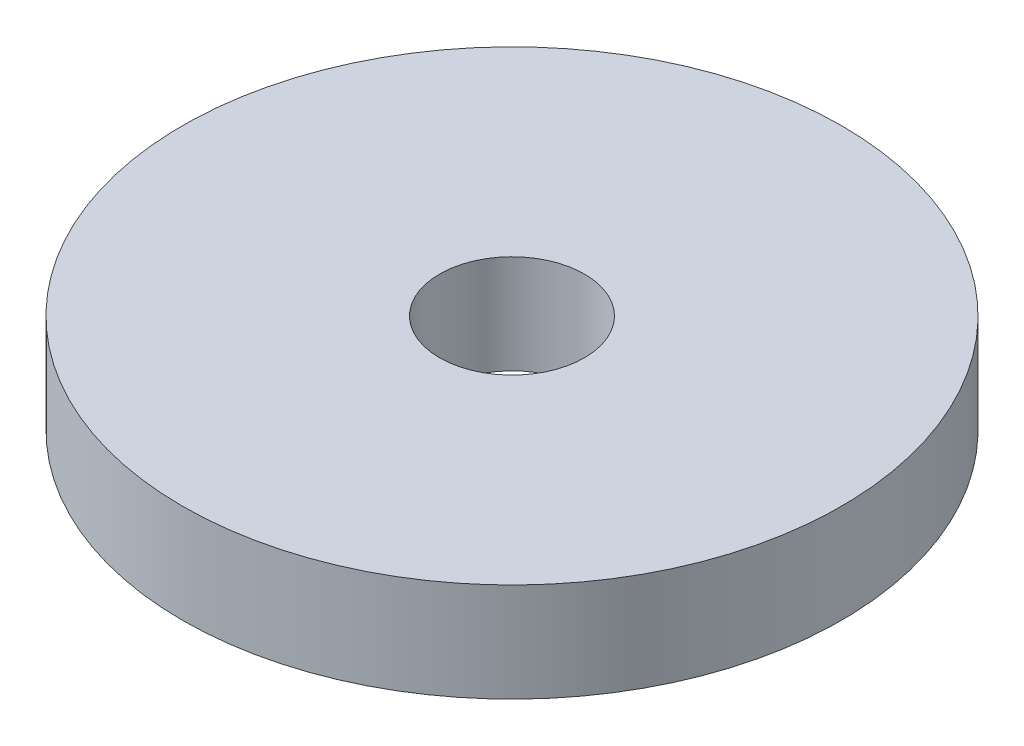
SolidWorks part; units mm, degrees
ref_plane "Front" through (0, 0, 0) normal (0, 0, 1) x (1, 0, 0)
ref_plane "Top" through (0, 0, 0) normal (0, 1, 0) x (1, 0, 0)
ref_plane "Right" through (0, 0, 0) normal (1, 0, 0) x (0, 0, -1)
sketch "Sketch1" plane through (0, 0, 0) normal (0, 1, 0) x (1, 0, 0)
  circle A0 centre (0, 0) radius 5
  circle A1 centre (0, 0) radius 1.1
  dimension "D1" = 2.2
  dimension "D2" = 10
extrude "Boss-Extrude1" add sketch "Sketch1" along normal blind 1.5
